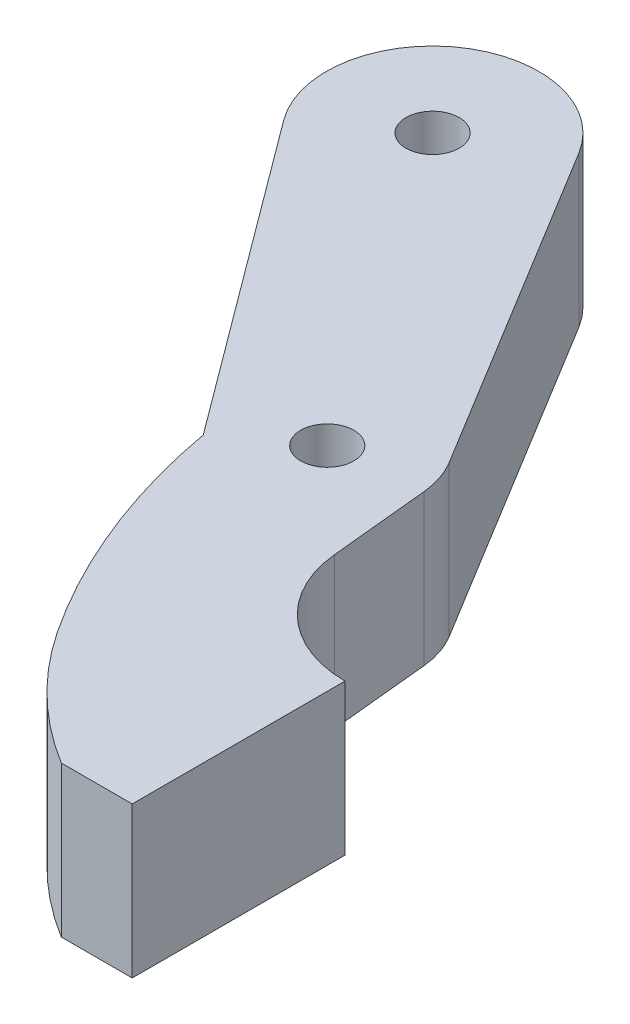
SolidWorks part; units mm, degrees
ref_plane "Alzado" through (0, 0, 0) normal (0, 0, 1) x (1, 0, 0)
ref_plane "Planta" through (0, 0, 0) normal (0, 1, 0) x (1, 0, 0)
ref_plane "Vista lateral" through (0, 0, 0) normal (1, 0, 0) x (0, 0, -1)
sketch "Croquis1" plane through (0, 0, 0) normal (0, 1, 0) x (1, 0, 0)
  line L0 (0, 0) -> (0, 73.7286) construction
  line L1 (0, 0) -> (-66.6175, 0) construction
  line L2 (-12, 15) -> (-70.2869, 15) construction
  line L3 (-12, 15) -> (-24.3022, 33.2388) construction
  line L4 (-29.1188, 29.661) -> (-16.0138, 12.0185)
  line L5 (-19.1807, 36.3644) -> (-7.732, 17.6047)
  line L6 (0, 4) -> (0, -8) construction
  line L7 (-6.4686, 9.8616) -> (-7.0242, 15.4911)
  line L8 (0, -8) -> (-4, -8)
  line L9 (0, 4) -> (0, -8)
  circle A0 centre (-24.3022, 33.2388) radius 1.5
  circle A1 centre (-12, 15) radius 1.5
  circle A2 centre (-24.3022, 33.2388) radius 6 construction
  circle A3 centre (-12, 15) radius 5 construction
  arc A4 (0, 4) -> (-6.4686, 9.8616) centre (0, 10.5) cw
  arc A5 (-4, -8) -> (-10.5, -1.7196) centre (7, 9.8885) cw
  arc A6 (-10.5, -1.7196) -> (-16.0138, 12.0185) centre (19.944, 18.4747) cw
  arc A7 (-29.1188, 29.661) -> (-19.1807, 36.3644) centre (-24.3022, 33.2388) cw
  arc A8 (-7.0242, 15.4911) -> (-7.732, 17.6047) centre (-12, 15) ccw
  dimension "D3" = 3
  dimension "D6" = 10
  dimension "D7" = 12
  dimension "D11" = 6.5
  dimension "D12" = 21
  dimension "D1" = 22
  dimension "D2" = 56
  dimension "D4" = 15
  dimension "D5" = 12
  dimension "D8" = 12
  dimension "D9" = 4
  dimension "D10" = 4
  dimension "D13" = 7
  dimension "D14" = 6.5
extrude "Saliente-Extruir1" add sketch "Croquis1" along normal blind 8.5
